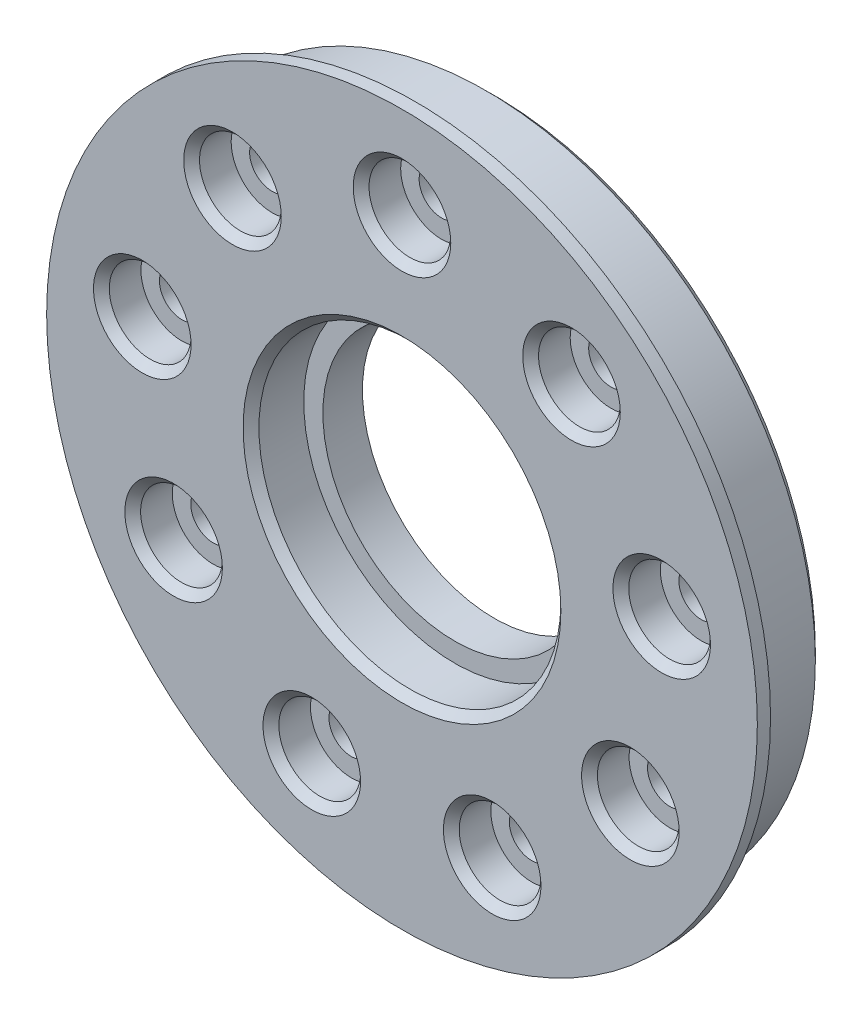
SolidWorks part; units mm, degrees
material "ABS"
ref_plane "Plan de face" through (0, 0, 0) normal (0, 0, 1) x (1, 0, 0)
ref_plane "Plan de dessus" through (0, 0, 0) normal (0, 1, 0) x (1, 0, 0)
ref_plane "Plan de droite" through (0, 0, 0) normal (1, 0, 0) x (0, 0, -1)
sketch "Esquisse1" plane through (0, 0, 0) normal (0, 0, 1) x (1, 0, 0)
  circle A0 centre (0, 0) radius 24.95
  dimension "D1" = 49.9
extrude "Boss.-Extru.1" add sketch "Esquisse1" along normal blind 6
sketch "Esquisse2" plane through (0, 0, 6) normal (0, 0, 1) x (1, 0, 0)
  circle A0 centre (0, 0) radius 26.95
  circle A1 centre (0, 0) radius 24.95 construction
  dimension "D1" = 2
extrude "Boss.-Extru.2" add sketch "Esquisse2" along normal blind 1
sketch "Esquisse3" plane through (0, 0, 7) normal (0, 0, -1) x (-1, 0, 0)
  circle A0 centre (0, 0) radius 20 construction
  circle A1 centre (0, 20) radius 3.1
  circle A2 centre (12.8558, 15.3209) radius 3.1
  circle A3 centre (19.6962, 3.473) radius 3.1
  circle A4 centre (17.3205, -10) radius 3.1
  circle A5 centre (6.8404, -18.7939) radius 3.1
  circle A6 centre (-6.8404, -18.7939) radius 3.1
  circle A7 centre (-17.3205, -10) radius 3.1
  circle A8 centre (-19.6962, 3.473) radius 3.1
  circle A9 centre (-12.8558, 15.3209) radius 3.1
  point P23 (0, 0)
  dimension "D1" = 6.2
  dimension "D3" = 40
  dimension "D2" = 9
extrude "Enlèv. mat.-Extru.1" cut sketch "Esquisse3" along normal blind 3
sketch "Esquisse4" plane through (0, 0, 0) normal (0, 0, -1) x (-1, 0, 0)
  circle A0 centre (0, 0) radius 20 construction
  circle A1 centre (0, 20) radius 1.7
  circle A2 centre (12.8558, 15.3209) radius 1.7
  circle A3 centre (19.6962, 3.473) radius 1.7
  circle A4 centre (17.3205, -10) radius 1.7
  circle A5 centre (6.8404, -18.7939) radius 1.7
  circle A6 centre (-6.8404, -18.7939) radius 1.7
  circle A7 centre (-17.3205, -10) radius 1.7
  circle A8 centre (-19.6962, 3.473) radius 1.7
  circle A9 centre (-12.8558, 15.3209) radius 1.7
  point P23 (0, 0)
  dimension "D1" = 40
  dimension "D2" = 3.4
  dimension "D3" = 9
extrude "Enlèv. mat.-Extru.2" cut sketch "Esquisse4" against normal through all
sketch "Esquisse5" plane through (0, 0, 7) normal (0, 0, 1) x (1, 0, 0)
  circle A0 centre (0, 0) radius 11.45
  dimension "D1" = 22.9
extrude "Enlèv. mat.-Extru.3" cut sketch "Esquisse5" against normal blind 4
sketch "Esquisse6" plane through (0, 0, 3) normal (0, 0, 1) x (1, 0, 0)
  circle A0 centre (0, 0) radius 10
  dimension "D1" = 20
extrude "Enlèv. mat.-Extru.4" cut sketch "Esquisse6" against normal through all
chamfer "Chanfrein1" distance 0.6 angle 45 10 edges at (-3.1, 20, 7) (9.7558, 15.3209, 7) (16.5962, 3.473, 7) (14.2205, -10, 7) (3.7404, -18.7939, 7) (-9.9404, -18.7939, 7) (-20.4205, -10, 7) (-22.7962, 3.473, 7) (-15.9558, 15.3209, 7) (11.45, 0, 7)
chamfer "Chanfrein2" distance 0.6 angle 45 1 edges at (24.95, 0, 0)
